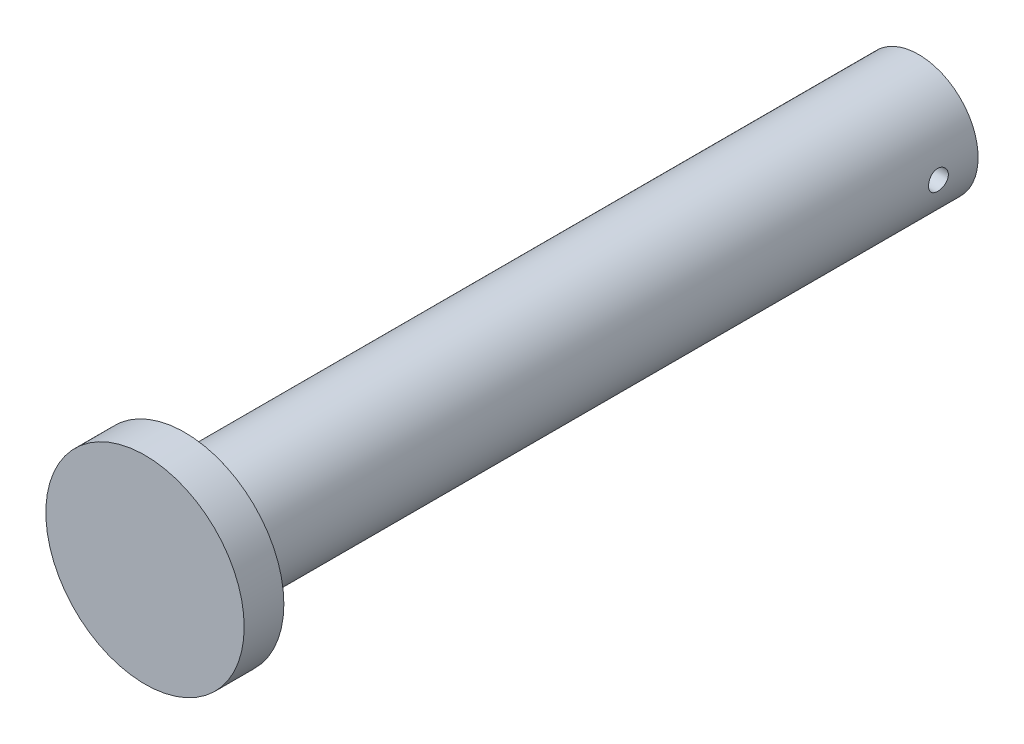
SolidWorks part; units mm, degrees
ref_plane "Front Plane" through (0, 0, 0) normal (0, 0, 1) x (1, 0, 0)
ref_plane "Top Plane" through (0, 0, 0) normal (0, 1, 0) x (1, 0, 0)
ref_plane "Right Plane" through (0, 0, 0) normal (1, 0, 0) x (0, 0, -1)
sketch "Sketch1" plane through (0, 0, 0) normal (0, 0, 1) x (1, 0, 0)
  circle A0 centre (0, 0) radius 25
  dimension "D1" = 50
extrude "Boss-Extrude1" add sketch "Sketch1" along normal blind 10
sketch "Sketch5" plane through (0, 0, 0) normal (0, 0, -1) x (-1, 0, 0)
  circle A0 centre (0, 0) radius 15
  dimension "D1" = 30
extrude "Boss-Extrude3" add sketch "Sketch5" along normal blind 185
sketch "Sketch6" plane through (0, 0, 0) normal (1, 0, 0) x (0, 0, -1)
  line L1 (185, -15) -> (185, 15) construction
  circle A0 centre (175, 0) radius 2.5
  dimension "D2" = 5
  dimension "D1" = 10
extrude "Cut-Extrude1" cut sketch "Sketch6" against normal mid plane 185
